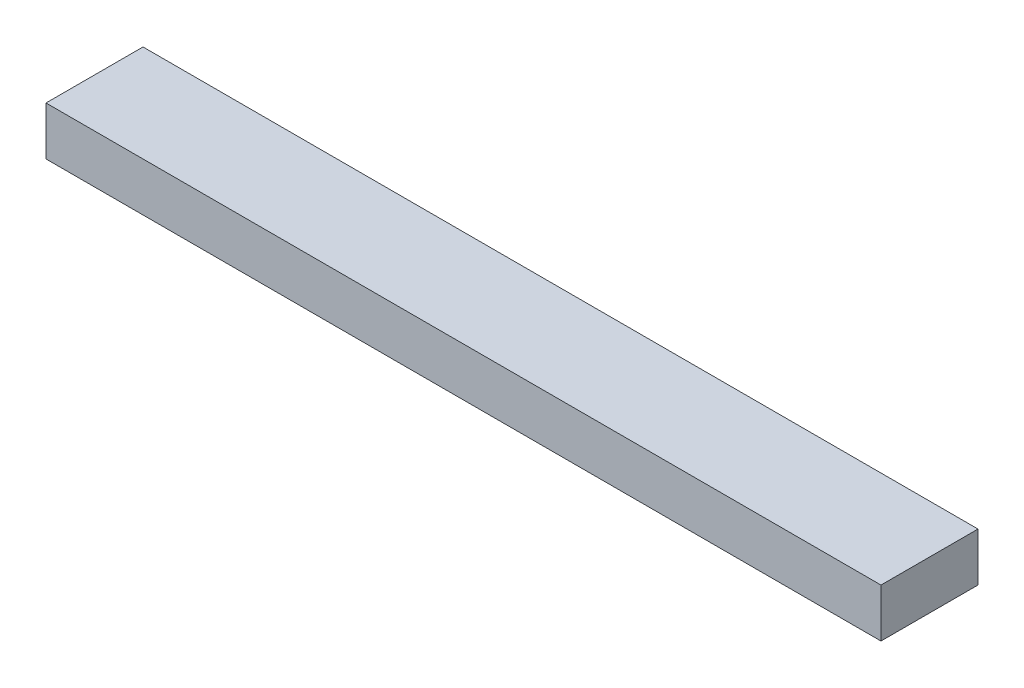
SolidWorks part; units mm, degrees
ref_plane "Front Plane" through (0, 0, 0) normal (0, 0, 1) x (1, 0, 0)
ref_plane "Top Plane" through (0, 0, 0) normal (0, 1, 0) x (1, 0, 0)
ref_plane "Right Plane" through (0, 0, 0) normal (1, 0, 0) x (0, 0, -1)
sketch "Sketch1" plane through (0, 0, 0) normal (0, 1, 0) x (1, 0, 0)
  line L1 (-437.1975, -50.8) -> (437.1975, -50.8)
  line L2 (-437.1975, -50.8) -> (-437.1975, 50.8)
  line L3 (-437.1975, 50.8) -> (437.1975, 50.8)
  line L4 (437.1975, -50.8) -> (437.1975, 50.8)
  line L5 (-437.1975, -50.8) -> (437.1975, 50.8) construction
  line L6 (-437.1975, 50.8) -> (437.1975, -50.8) construction
  point P0 (0, 0)
  dimension "D1" = 101.6
  dimension "D2" = 874.395
extrude "Boss-Extrude1" add sketch "Sketch1" along normal mid plane 50.8
